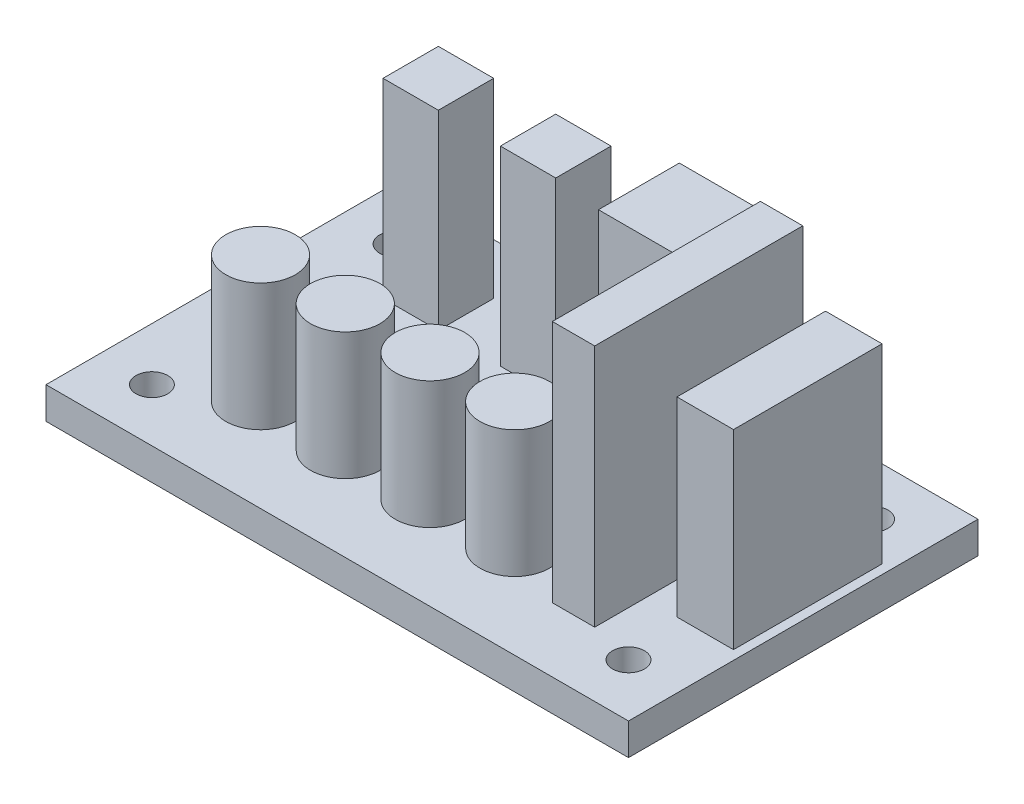
SolidWorks part; units mm, degrees
ref_plane "Face" through (0, 0, 0) normal (0, 0, 1) x (1, 0, 0)
ref_plane "Dessus" through (0, 0, 0) normal (0, 1, 0) x (1, 0, 0)
ref_plane "Droite" through (0, 0, 0) normal (1, 0, 0) x (0, 0, -1)
sketch "Esquisse1" plane through (0, 0, 0) normal (0, 1, 0) x (1, 0, 0)
  line L0 (0, 16.5) -> (55, 16.5) construction
  line L1 (0, 0) -> (55, 0)
  line L2 (0, 0) -> (0, 33)
  line L3 (0, 33) -> (55, 33)
  line L4 (55, 0) -> (55, 33)
  line L5 (27.5, 33) -> (27.5, 0) construction
  circle A0 centre (5, 28) radius 1.5
  circle A1 centre (50, 28) radius 1.5
  circle A2 centre (50, 5) radius 1.5
  circle A3 centre (5, 5) radius 1.5
  dimension "D3" = 3
  dimension "D1" = 33
  dimension "D2" = 55
  dimension "D4" = 5
  dimension "D5" = 5
extrude "Extrusion1" add sketch "Esquisse1" along normal blind 3
sketch "Esquisse2" plane through (0, 3, 0) normal (0, 1, 0) x (1, 0, 0)
  line L1 (29.7763, 30.0228) -> (37.4105, 30.0228)
  line L2 (29.7763, 30.0228) -> (29.7763, 22.3886)
  line L3 (29.7763, 22.3886) -> (37.4105, 22.3886)
  line L4 (37.4105, 30.0228) -> (37.4105, 22.3886)
  line L5 (48.7885, 24.8147) -> (54.1263, 24.8147)
  line L6 (48.7885, 24.8147) -> (48.7885, 10.7874)
  line L7 (48.7885, 10.7874) -> (54.1263, 10.7874)
  line L8 (54.1263, 24.8147) -> (54.1263, 10.7874)
  line L13 (8.8572, 28.1893) -> (14.0816, 28.1893)
  line L14 (8.8572, 28.1893) -> (8.8572, 22.965)
  line L15 (8.8572, 22.965) -> (14.0816, 22.965)
  line L16 (14.0816, 28.1893) -> (14.0816, 22.965)
  line L17 (19.94, 28.1893) -> (25.1643, 28.1893)
  line L18 (19.94, 28.1893) -> (19.94, 22.965)
  line L19 (19.94, 22.965) -> (25.1643, 22.965)
  line L20 (25.1643, 28.1893) -> (25.1643, 22.965)
extrude "Extrusion2" add sketch "Esquisse2" along normal blind 18
sketch "Esquisse3" plane through (0, 3, 0) normal (0, 1, 0) x (1, 0, 0)
  line L0 (0, 8.7568) -> (55, 8.7568) construction
  line L1 (0, 33) -> (0, 0) construction
  line L2 (55, 0) -> (55, 33) construction
  circle A0 centre (11.5, 8.7568) radius 3.2791
  circle A1 centre (19.5, 8.7568) radius 3.2791
  circle A2 centre (27.5, 8.7568) radius 3.2791
  circle A3 centre (35.5, 8.7568) radius 3.2791
  dimension "D1" = 8
  dimension "D2" = 8
  dimension "D3" = 8
extrude "Extrusion3" add sketch "Esquisse3" along normal blind 12
sketch "Esquisse4" plane through (0, 3, 0) normal (0, 1, 0) x (1, 0, 0)
  line L1 (41.7375, 25.7183) -> (45.7375, 25.7183)
  line L2 (41.7375, 25.7183) -> (41.7375, 6.0722)
  line L3 (41.7375, 6.0722) -> (45.7375, 6.0722)
  line L4 (45.7375, 25.7183) -> (45.7375, 6.0722)
  dimension "D1" = 4
extrude "Extrusion4" add sketch "Esquisse4" along normal blind 23
